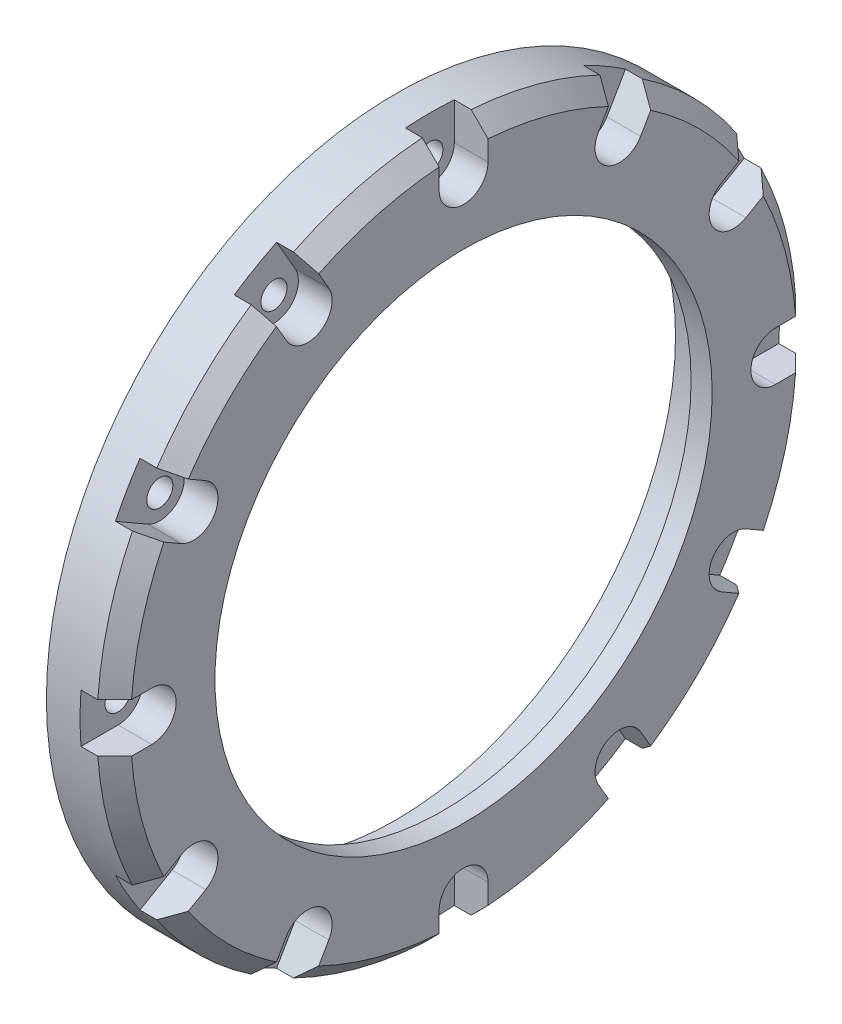
SolidWorks part; units mm, degrees
material "6061 合金"
ref_plane "前视基准面" through (0, 0, 0) normal (0, 0, 1) x (1, 0, 0)
ref_plane "上视基准面" through (0, 0, 0) normal (0, 1, 0) x (1, 0, 0)
ref_plane "右视基准面" through (0, 0, 0) normal (1, 0, 0) x (0, 0, -1)
sketch "草图1" plane through (0, 0, 0) normal (1, 0, 0) x (0, 0, -1)
  circle A0 centre (0, 0) radius 33.15
  circle A1 centre (0, 0) radius 41.5
  dimension "D1" = 66.3
  dimension "D2" = 83
extrude "凸台-拉伸1" add sketch "草图1" along normal blind 8
sketch "草图2" plane through (0, 0, 0) normal (-1, 0, 0) x (0, 0, 1)
  line L0 (0, 37) -> (0, 0) construction
  circle A0 centre (0, 37) radius 1.55
  circle A2 centre (0, 0) radius 33.15 construction
  dimension "D2" = 3.1
  dimension "D1" = 37
extrude "切除-拉伸1" cut sketch "草图2" against normal blind 8
pattern_circular "阵列(圆周)1" count 12 over 360 about axis through (0, 0, 0) along (1, 0, 0) of "切除-拉伸1"
sketch "草图3" plane through (8, 0, 0) normal (1, 0, 0) x (0, 0, -1)
  circle A0 centre (0, 0) radius 33.15
  circle A1 centre (0, 0) radius 29.5
  circle A4 centre (0, 0) radius 33.15 construction
  dimension "D1" = 66.3
  dimension "D2" = 59
extrude "凸台-拉伸2" add sketch "草图3" against normal blind 2.5
chamfer "倒角1" distance 2 angle 45 1 edges at (8, 0, -41.5)
sketch "草图4" plane through (8, 0, 0) normal (1, 0, 0) x (0, 0, -1)
  line L0 (37, 0) -> (45, 0) construction
  line L1 (37, 2.9) -> (45, 2.9)
  line L2 (37, -2.9) -> (45, -2.9)
  arc A5 (37, 2.9) -> (37, -2.9) centre (37, 0) ccw
  arc A6 (45, -2.9) -> (45, 2.9) centre (45, 0) ccw
  circle A9 centre (37, 0) radius 1.55 construction
  point P2 (41, 0)
  dimension "D1" = 2.9
  dimension "D2" = 8
extrude "切除-拉伸8" cut sketch "草图4" against normal blind 4
pattern_circular "阵列(圆周)7" count 12 over 360 about axis through (0, 0, 0) along (1, 0, 0) of "切除-拉伸8"
